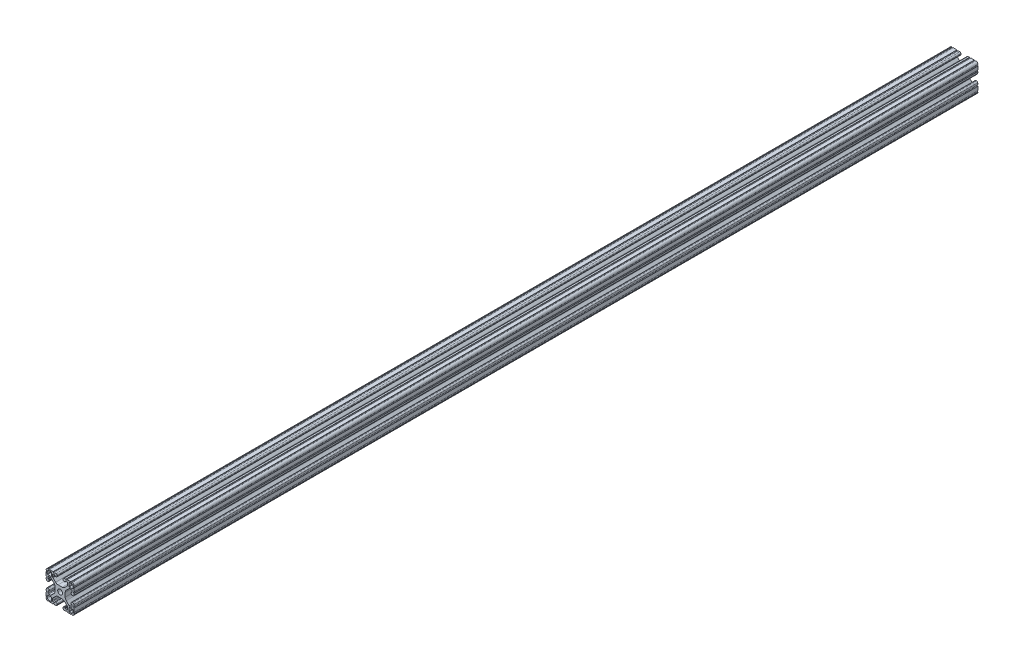
SolidWorks part; units mm, degrees
ref_plane "Front Plane" through (0, 0, 0) normal (0, 0, 1) x (1, 0, 0)
ref_plane "Top Plane" through (0, 0, 0) normal (0, 1, 0) x (1, 0, 0)
ref_plane "Right Plane" through (0, 0, 0) normal (1, 0, 0) x (0, 0, -1)
sketch "Sketch2" plane through (0, 0, 0) normal (0, 0, 1) x (1, 0, 0)
  line L0 (0, 19.05) -> (0, -19.05) construction
  line L1 (-19.05, 0) -> (19.05, 0) construction
  line L2 (4.064, -19.05) -> (19.05, -19.05) construction
  line L3 (19.05, -19.05) -> (19.05, -4.064) construction
  line L4 (4.064, -19.05) -> (4.064, -15.8768) construction
  line L5 (4.064, -15.8768) -> (13.7215, -15.8768) construction
  line L6 (13.7215, -15.8768) -> (4.7027, -6.858) construction
  line L7 (0, 0) -> (19.05, -19.05) construction
  line L8 (19.05, -4.064) -> (15.8768, -4.064) construction
  line L9 (15.8768, -4.064) -> (15.8768, -13.7215) construction
  line L10 (15.8768, -13.7215) -> (6.858, -4.7027) construction
  line L11 (11.3674, -9.2121) -> (9.2121, -11.3674) construction
  line L12 (10.287, -12.4423) -> (10.287, -15.8768) construction
  line L13 (15.7642, -19.0481) -> (4.064, -18.6395) construction
  line L14 (4.064, -18.6395) -> (4.2014, -14.7049) construction
  line L15 (4.2014, -14.7049) -> (6.858, -14.7977) construction
  line L16 (6.858, -14.7977) -> (6.858, -15.8768) construction
  line L17 (19.05, 4.064) -> (19.05, -4.064) construction
  line L18 (-19.05, -19.05) -> (19.05, -19.05) construction
  line L19 (-19.05, -19.05) -> (-19.05, 19.05) construction
  line L20 (-19.05, 19.05) -> (19.05, 19.05) construction
  line L21 (19.05, -19.05) -> (19.05, 19.05) construction
  line L22 (8.5725, -18.7969) -> (8.6004, -17.9973) construction
  line L23 (15.24, -19.0298) -> (15.2679, -18.2301) construction
  circle A0 centre (0, 0) radius 3.2639 construction
  arc A1 (18.1201, -18.1201) -> (15.7642, -19.0481) centre (15.875, -15.875) cw construction
  point P8 (0, -6.858)
  point P16 (10.2898, -10.2898)
  point P28 (11.8872, -11.8872)
  point P34 (8.5725, -18.7969)
  point P36 (15.24, -19.0298)
  point P38 (19.05, 0)
  dimension "D7" = 1.6002
  dimension "Center Hole Diameter" = 6.5278
  dimension "Corner Radius" = 3.175
  dimension "Slot Depth" = 12.192
  dimension "D1" = 3.048
  dimension "D3" = 2
  dimension "Flange Thickness" = 3.937
  dimension "D4" = 3.1732
  dimension "D2" = 20.574
  dimension "D5" = 13.716
  dimension "D6" = 7.1628
  dimension "D8" = 15.24
  dimension "D9" = 8.5725
  dimension "D10" = 0.8001
  dimension "Rail Height" = 38.1
  dimension "Rail Width" = 38.1
  dimension "T Slot Width" = 8.128
sketch "Sketch3" plane through (0, 0, 0) normal (1, 0, 0) x (0, 0, -1)
  line L0 (-609.6, 19.05) -> (609.6, 19.05) construction
  line L1 (-558.8, 0) -> (558.8, 0) construction
  dimension "Length" = 1219.2
  dimension "D1" = 50.8
sketch "Sketch4" plane through (0, 0, 0) normal (0, 0, 1) x (1, 0, 0)
  line L1 (6.858, -14.7977) -> (6.858, -15.8768) construction
  line L2 (11.8872, -12.2682) -> (11.8872, -16.9436)
  line L3 (12.2549, -17.3243) -> (14.4454, -17.4008)
  line L7 (12.2682, -11.8872) -> (16.9436, -11.8872)
  line L9 (17.3243, -12.2549) -> (17.4008, -14.4454)
  line L22 (0, 0) -> (19.05, -19.05) construction
  line L23 (15.7642, -19.0481) -> (5.5961, -18.693)
  line L24 (4.064, -17.1065) -> (4.064, -16.344)
  line L25 (5.7069, -14.7575) -> (6.4903, -14.7848)
  line L26 (6.858, -15.1656) -> (6.858, -15.6891)
  line L27 (7.2257, -16.0699) -> (9.4655, -16.1481)
  line L28 (10.287, -15.3549) -> (10.287, -12.771)
  line L29 (10.0545, -12.2098) -> (6.0939, -8.2492)
  line L30 (2.7353, -6.858) -> (0, -6.858)
  line L31 (13.7215, -15.8768) -> (4.7027, -6.858) construction
  line L32 (4.064, -19.05) -> (19.05, -19.05) construction
  line L33 (4.064, -19.05) -> (4.064, -15.8768) construction
  line L34 (0, 19.05) -> (0, -19.05) construction
  line L35 (0, -3.2639) -> (0, -6.858)
  line L36 (0, 0) -> (19.1669, -19.1669) construction
  line L46 (10.287, -12.4423) -> (10.287, -15.8768) construction
  line L47 (6.858, -2.7353) -> (6.858, 0)
  line L48 (12.2098, -10.0545) -> (8.2492, -6.0939)
  line L49 (15.3549, -10.287) -> (12.771, -10.287)
  line L50 (16.0699, -7.2257) -> (16.1481, -9.4655)
  line L51 (15.1656, -6.858) -> (15.6891, -6.858)
  line L52 (14.7575, -5.7069) -> (14.7848, -6.4903)
  line L53 (17.1065, -4.064) -> (16.344, -4.064)
  line L54 (19.0481, -15.7642) -> (18.693, -5.5961)
  line L55 (3.2639, 0) -> (6.858, 0)
  arc A1 (14.4454, -17.4008) -> (17.4008, -14.4454) centre (14.5451, -14.5451) ccw
  arc A10 (16.9436, -11.8872) -> (17.3243, -12.2549) centre (16.9436, -12.2682) cw
  arc A12 (19.0481, -15.7642) -> (15.7642, -19.0481) centre (15.875, -15.875) cw
  arc A13 (3.2639, 0) -> (0, -3.2639) centre (0, 0) cw
  circle A14 centre (0, 0) radius 3.2639 construction
  arc A16 (6.0939, -8.2492) -> (2.7353, -6.858) centre (2.7353, -11.6078) ccw
  arc A17 (5.5961, -18.693) -> (4.064, -17.1065) centre (5.6515, -17.1065) cw
  arc A18 (4.064, -16.344) -> (5.7069, -14.7575) centre (5.6515, -16.344) cw
  arc A19 (9.4655, -16.1481) -> (10.287, -15.3549) centre (9.4933, -15.3549) ccw
  arc A20 (10.287, -12.771) -> (10.0545, -12.2098) centre (9.4933, -12.771) ccw
  arc A21 (6.4903, -14.7848) -> (6.858, -15.1656) centre (6.477, -15.1656) cw
  arc A22 (6.858, -15.6891) -> (7.2257, -16.0699) centre (7.239, -15.6891) ccw
  arc A23 (15.6891, -6.858) -> (16.0699, -7.2257) centre (15.6891, -7.239) cw
  arc A24 (14.7848, -6.4903) -> (15.1656, -6.858) centre (15.1656, -6.477) ccw
  arc A25 (12.771, -10.287) -> (12.2098, -10.0545) centre (12.771, -9.4933) cw
  arc A26 (16.1481, -9.4655) -> (15.3549, -10.287) centre (15.3549, -9.4933) cw
  arc A27 (16.344, -4.064) -> (14.7575, -5.7069) centre (16.344, -5.6515) ccw
  arc A28 (18.693, -5.5961) -> (17.1065, -4.064) centre (17.1065, -5.6515) ccw
  arc A29 (8.2492, -6.0939) -> (6.858, -2.7353) centre (11.6078, -2.7353) cw
  arc A30 (15.7642, -19.0481) -> (18.1201, -18.1201) centre (15.875, -15.875) ccw construction
  arc A31 (11.8872, -12.2682) -> (12.2682, -11.8872) centre (12.2682, -12.2682) cw
  arc A32 (11.8872, -16.9436) -> (12.2549, -17.3243) centre (12.2682, -16.9436) ccw
  point P33 (4.064, -18.6395)
  point P42 (6.858, -4.7027)
  point P45 (4.7027, -6.858)
  point P76 (18.6395, -4.064)
  point P89 (11.8872, -11.8872)
  dimension "D2" = 4.7498
  dimension "D3" = 0.7937
  dimension "D5" = 0.381
  dimension "D6" = 1.5875
  dimension "D8" = 2.8575
  dimension "D1" = 2
  dimension "D4" = 2.6784
  dimension "D7" = 1.6002
extrude "Boss-Extrude1" add sketch "Sketch4" along normal mid plane 1219.2
sketch "Sketch8" plane through (0, 0, 0) normal (0, 0, 1) x (1, 0, 0)
  line L0 (7.6492, -18.7647) -> (9.4958, -18.8292)
  line L1 (15.7642, -19.0481) -> (4.064, -18.6395) construction
  line L2 (9.4958, -18.8292) -> (9.2789, -18.4213)
  line L3 (7.894, -18.3729) -> (7.6492, -18.7647)
  line L4 (8.5725, -18.7969) -> (8.6004, -17.9973) construction
  line L5 (14.3167, -18.9975) -> (16.1633, -19.062)
  line L7 (16.1633, -19.062) -> (15.9464, -18.6541)
  line L8 (14.5615, -18.6058) -> (14.3167, -18.9975)
  line L9 (15.24, -19.0298) -> (15.2679, -18.2301) construction
  line L10 (0, 0) -> (19.05, -19.05) construction
  line L11 (18.6058, -14.5615) -> (18.9975, -14.3167)
  line L12 (19.062, -16.1633) -> (18.6541, -15.9464)
  line L13 (18.9975, -14.3167) -> (19.062, -16.1633)
  line L14 (18.3729, -7.894) -> (18.7647, -7.6492)
  line L15 (18.8292, -9.4958) -> (18.4213, -9.2789)
  line L16 (18.7647, -7.6492) -> (18.8292, -9.4958)
  arc A0 (9.2789, -18.4213) -> (7.894, -18.3729) centre (8.5725, -18.7969) ccw
  arc A1 (15.9464, -18.6541) -> (14.5615, -18.6058) centre (15.24, -19.0298) ccw
  arc A2 (18.6541, -15.9464) -> (18.6058, -14.5615) centre (19.0298, -15.24) cw
  arc A3 (18.4213, -9.2789) -> (18.3729, -7.894) centre (18.7969, -8.5725) cw
  dimension "D1" = 60
extrude "Cut-Extrude2" cut sketch "Sketch8" against normal through all both and the other way through all
mirror "Mirror1" about plane through (0, 0, 0) normal (1, 0, 0) of bodies 142 134
mirror "Mirror2" about plane through (0, 0, 0) normal (0, 1, 0) of bodies 135
sketch "Sketch5" plane through (0, 0, 0) normal (0, 0, 1) x (1, 0, 0)
  line L0 (-6.0939, 8.2492) -> (-10.0545, 12.2098) construction
  line L1 (-10.1338, 12.508) -> (-10.1338, 12)
  line L2 (-9.9645, 11.8306) -> (-9.6506, 11.8306)
  line L3 (-9.6506, 11.8306) -> (-9.6506, 12.508)
  line L4 (-9.6506, 12.508) -> (-10.1338, 12.508)
  line L5 (-9.9046, 12.0598) -> (-9.9645, 12) construction
  circle A0 centre (-9.9046, 12.0598) radius 0.254 construction
  arc A1 (-10.287, 12.771) -> (-10.0545, 12.2098) centre (-9.4933, 12.771) ccw construction
  arc A2 (-10.1338, 12) -> (-9.9645, 11.8306) centre (-9.9645, 12) ccw
  dimension "D2" = 0.508
  dimension "D3" = 0.1693
  dimension "D1" = 0.7112
  dimension "D4" = 0.508
extrude "Cut-Extrude1" cut sketch "Sketch5" against normal through all both and the other way through all
ref_plane "Plane1" through (0, 19.05, 0) normal (0, 1, 0) x (-1, 0, 0)
ref_plane "Plane2" through (19.05, 0, 0) normal (1, 0, 0) x (0, 0, -1)
ref_plane "Plane3" through (0, -19.05, 0) normal (0, -1, 0) x (1, 0, 0)
ref_plane "Plane4" through (-19.05, 0, 0) normal (-1, 0, 0) x (0, 0, 1)
equation "\"D1@Boss-Extrude1\"=\"Length@Sketch3\""
equation "\"D6@Sketch4\"=\"Corner Radius@Sketch2\"/2"
equation "\"D3@Sketch4\"=\"D6@Sketch4\"/2"
equation "\"D4@Sketch2\"=\"Flange Thickness@Sketch2\"*.806"
equation "\"D7@Sketch4\"=\"D7@Sketch2\""
equation "\"D8@Sketch4\"=\"Corner Radius@Sketch2\"*.9"
equation "\"D3@Sketch5\"=\"D2@Sketch5\"/3"
equation "\"D4@Sketch5\"=\"D2@Sketch5\""
equation "\"D8@Sketch2\"=\"Rail Width@Sketch2\"*.4"
equation "\"D9@Sketch2\"=\"Rail Width@Sketch2\"*.225"
equation "\"D10@Sketch2\"=\"D7@Sketch2\"/2"
